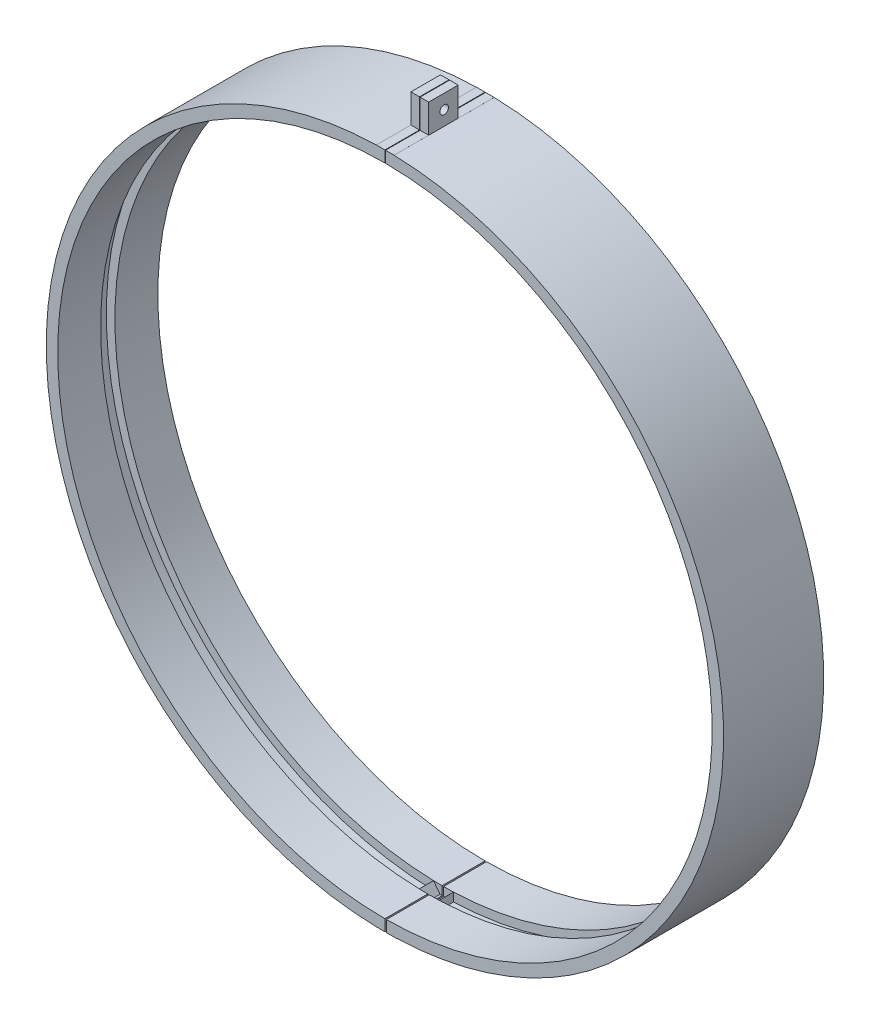
SolidWorks part; units mm, degrees
material "6063-T4"
ref_plane "Front Plane" through (0, 0, 0) normal (0, 0, 1) x (1, 0, 0)
ref_plane "Top Plane" through (0, 0, 0) normal (0, 1, 0) x (1, 0, 0)
ref_plane "Right Plane" through (0, 0, 0) normal (1, 0, 0) x (0, 0, -1)
sketch "Sketch1" plane through (0, 0, 0) normal (0, 0, 1) x (1, 0, 0)
  circle A0 centre (0, 0) radius 114.4
  circle A1 centre (0, 0) radius 118.4
extrude "Extrude1" add sketch "Sketch1" along normal blind 15
sketch "Sketch2" plane through (0, 0, 15) normal (0, 0, 1) x (1, 0, 0)
  circle A0 centre (0, 0) radius 118.4
  circle A1 centre (0, 0) radius 117.4
  point P0 (0, 0)
extrude "Extrude2" add sketch "Sketch2" along normal blind 5
sketch "Sketch3" plane through (0, 0, 20) normal (0, 0, 1) x (1, 0, 0)
  circle A0 centre (0, 0) radius 118.4
  circle A1 centre (0, 0) radius 114.4
  point P0 (0, 0)
extrude "Extrude3" add sketch "Sketch3" along normal blind 15
sketch "Sketch4" plane through (0, 0, 35) normal (0, 0, 1) x (1, 0, 0)
  line L0 (0, 0) -> (0, 118.4) construction
  line L1 (0, 0) -> (0, -118.4) construction
  line L2 (0, 118.4) -> (0, 128.4)
  line L3 (0, 128.4) -> (-3, 128.4)
  line L4 (-3, 128.4) -> (-3, 114.3607)
  line L5 (0, 128.4) -> (12.1071, 128.4) construction
  line L6 (0.2, 128.4) -> (0.2, 226.0706) construction
  line L7 (0.2, 128.4) -> (3.2, 128.4)
  line L8 (3.2, 128.4) -> (3.2, 114.3552)
  line L9 (3.2, 114.3552) -> (0.2, 118.3998)
  line L10 (0.2, 118.3998) -> (0.2, 128.4)
  line L11 (0, -118.4) -> (0, -260.7808) construction
  line L12 (0, -128.4) -> (-29.7007, -128.4) construction
  line L13 (0, -128.4) -> (32.692, -128.4) construction
  line L14 (0, -118.4) -> (0, -128.4)
  line L15 (0, -128.4) -> (-3, -128.4)
  line L16 (-3, -128.4) -> (-3, -114.3607)
  line L17 (-3, -114.3607) -> (0, -118.4)
  line L18 (0.5, -128.4) -> (0.5, -106.2676) construction
  line L19 (0.5, -118.3989) -> (0.5, -128.4)
  line L20 (0.5, -128.4) -> (4, -128.4)
  line L21 (4, -128.4) -> (4, -114.33)
  line L22 (4, -114.33) -> (0.5, -118.3989)
  circle A0 centre (0, 0) radius 114.4 construction
  circle A1 centre (0, 0) radius 114.4 construction
  circle A2 centre (0, 0) radius 118.4 construction
  arc A3 (-3, 114.3607) -> (0, 118.4) centre (1.2194, 114.3607) cw
  point P0 (109.4647, 33.239)
  point P1 (0, 0)
  point P8 (0, 114.4)
  point P15 (0.2, 128.4)
  point P19 (0.2, 118.3998)
  point P20 (3.2, 128.4)
  point P21 (0, -114.4)
  point P25 (0, -128.4)
  point P29 (-3, -128.4)
  point P31 (0.5, -128.4)
  point P32 (4, -128.4)
  point P37 (0.5, -118.3989)
  dimension "D1" = 10
  dimension "D2" = 3
  dimension "D3" = 0.2
  dimension "D4" = 3
  dimension "D5" = 10
extrude "Extrude4" add sketch "Sketch4" against normal blind 35
sketch "Sketch5" plane through (0, 0, 35) normal (0, 0, 1) x (1, 0, 0)
  line L0 (0, 0) -> (0, 128.4) construction
  line L1 (0, 128.4) -> (0.2, 128.4)
  line L3 (0.2, 128.4) -> (0.2, 110.7631)
  line L4 (0, 128.4) -> (0, 110.7631)
  line L5 (0, 110.7631) -> (0.2, 110.7631)
  line L6 (0, 0) -> (0, -128.4) construction
  line L7 (0, -128.4) -> (0.5, -128.4)
  line L8 (0.5, -128.4) -> (0.5, -107.1151)
  line L9 (0, -128.4) -> (0, -107.1151)
  line L10 (0, -107.1151) -> (0.5, -107.1151)
  point P0 (0, 0)
extrude "Extrude5" cut sketch "Sketch5" against normal through all
sketch "Sketch6" plane through (-3, 0, 0) normal (-1, 0, 0) x (0, 0, 1)
  line L0 (0, 128.4) -> (35, 128.4) construction
  line L1 (35, 128.4) -> (35, 118.362) construction
  line L2 (0, 128.4) -> (0, 118.362) construction
  line L3 (17.5, 118.362) -> (17.5, 128.4) construction
  line L4 (35, 118.362) -> (0, 118.362) construction
  line L5 (0, 123.381) -> (35, 123.381) construction
  line L6 (22.9144, 128.4) -> (35, 128.4)
  line L7 (35, 128.4) -> (35, 118.362)
  line L8 (35, 118.362) -> (22.9144, 118.362)
  line L9 (22.9144, 118.362) -> (22.9144, 128.4)
  line L10 (12.5824, 128.4) -> (12.5824, 118.362)
  line L11 (12.5824, 118.362) -> (0, 118.362)
  line L12 (0, 118.362) -> (0, 128.4)
  line L13 (0, 128.4) -> (12.5824, 128.4)
  line L15 (35, -118.362) -> (35, -128.4) construction
  line L16 (0, -118.362) -> (0, -128.4) construction
  line L17 (0, -128.4) -> (35, -128.4) construction
  line L18 (0, -118.362) -> (35, -118.362) construction
  line L19 (22.9144, -118.362) -> (35, -118.362)
  line L20 (35, -118.362) -> (35, -128.4)
  line L21 (35, -128.4) -> (22.9144, -128.4)
  line L22 (22.9144, -128.4) -> (22.9144, -118.362)
  line L23 (12.5824, -118.362) -> (12.5824, -128.4)
  line L24 (12.5824, -128.4) -> (0, -128.4)
  line L25 (0, -128.4) -> (0, -118.362)
  line L26 (0, -118.362) -> (12.5824, -118.362)
  circle A0 centre (17.5, 123.381) radius 1.5
  circle A1 centre (17.5, -123.381) radius 1.5
  point P0 (17.5, 128.4)
  point P1 (17.5, 236.7334)
  point P4 (35, 123.381)
  point P5 (0, 123.381)
  point P16 (17.5, 123.381)
  point P17 (17.5, -123.381)
  point P22 (12.5824, 128.4)
  point P23 (35, 118.362)
  point P24 (35, 128.4)
  point P25 (0, 118.362)
  point P26 (0, 128.4)
  point P28 (12.5824, 118.362)
  point P30 (22.9144, 128.4)
  point P31 (22.9144, 118.362)
  point P36 (35, -123.381)
  point P39 (0, -123.381)
  point P42 (17.5, -128.4)
  point P45 (17.5, -118.362)
  point P53 (22.9144, -128.4)
  point P54 (12.5824, -128.4)
  point P55 (22.9144, -118.362)
  point P56 (12.5824, -118.362)
  point P57 (35, -118.362)
  point P58 (35, -128.4)
  point P60 (0, -118.362)
  point P62 (0, -128.4)
extrude "Extrude6" cut sketch "Sketch6" against normal through all
